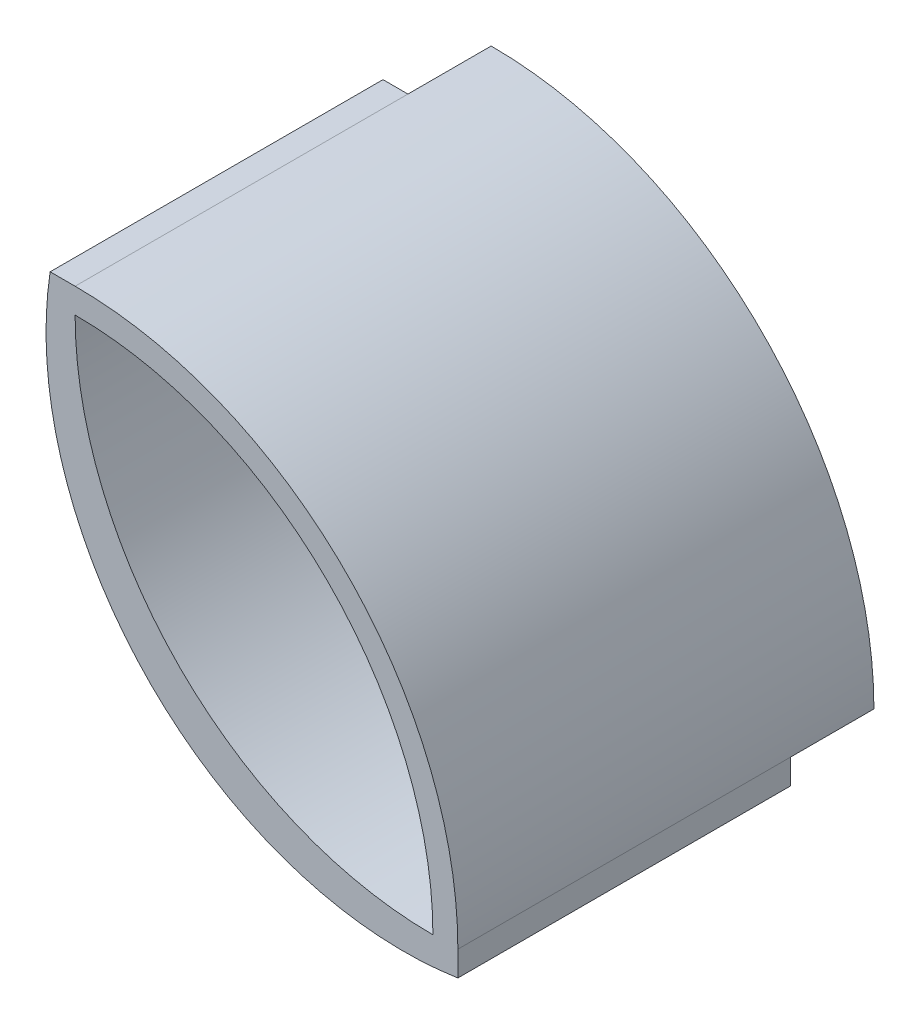
SolidWorks part; units mm, degrees
ref_plane "Front Plane" through (0, 0, 0) normal (0, 0, 1) x (1, 0, 0)
ref_plane "Top Plane" through (0, 0, 0) normal (0, 1, 0) x (1, 0, 0)
ref_plane "Right Plane" through (0, 0, 0) normal (1, 0, 0) x (0, 0, -1)
sketch "Sketch1" plane through (0, 0, 0) normal (0, 0, 1) x (1, 0, 0)
  line L0 (-170.5232, 0) -> (140.0827, 0) construction
  line L1 (0, 90.1941) -> (0, -90.1941) construction
  line L2 (0, 46) -> (0, 43)
  line L3 (43, 0) -> (46, 0)
  arc A0 (43, 0) -> (0, 43) centre (0, 0) ccw
  arc A1 (46, 0) -> (0, 46) centre (0, 0) ccw
extrude "Boss-Extrude1" add sketch "Sketch1" along normal blind 10
ref_plane "Plane1" through (0, 0, 10) normal (0, 0, 1) x (1, 0, 0)
sketch "Sketch3" plane through (0, 0, 10) normal (0, 0, 1) x (1, 0, 0)
  line L0 (0, 43) -> (43, 0) construction
  line L1 (0, 46) -> (-3, 46)
  line L2 (46, 0) -> (46, -3)
  line L3 (0, 46) -> (0, 43)
  line L4 (46, 0) -> (43, 0)
  arc A1 (0, 43) -> (43, 0) centre (43, 43) ccw
  arc A2 (46, -3) -> (-3, 46) centre (39.5069, 39.5069) cw
  dimension "D1" = 3
  dimension "D2" = 3
extrude "Boss-Extrude2" add sketch "Sketch3" along normal blind 40 separate body
ref_plane "Plane2" through (0, 0, 10) normal (0, 0, 1) x (1, 0, 0)
sketch "Sketch4" plane through (0, 0, 10) normal (0, 0, 1) x (1, 0, 0)
  line L0 (0, 46) -> (0, 43)
  line L1 (46, 0) -> (43, 0)
  arc A0 (0, 43) -> (43, 0) centre (0, 0) cw
  arc A1 (0, 46) -> (46, 0) centre (0, 0) cw
extrude "Boss-Extrude3" add sketch "Sketch4" along normal blind 40
